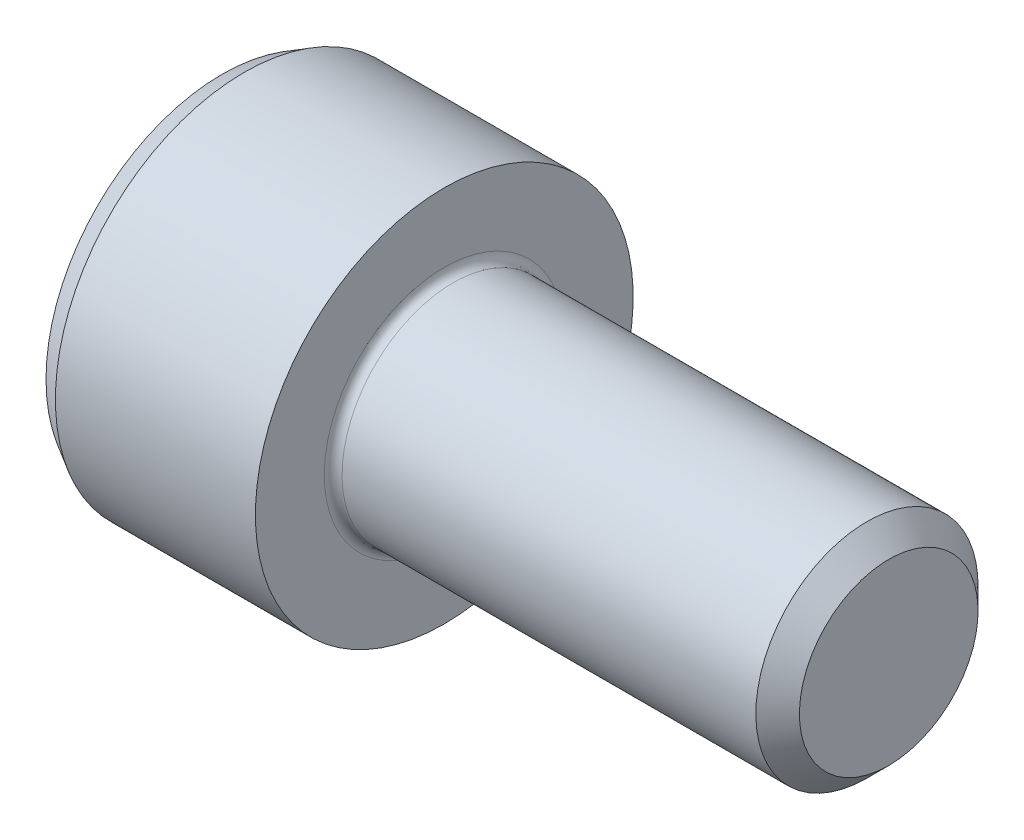
SolidWorks part; units mm, degrees
ref_plane "正面" through (0, 0, 0) normal (0, 0, 1) x (1, 0, 0)
ref_plane "平面" through (0, 0, 0) normal (0, 1, 0) x (1, 0, 0)
ref_plane "右側面" through (0, 0, 0) normal (1, 0, 0) x (0, 0, -1)
ref_plane "平面1" through (0, 0, 0) normal (0, 0, 1) x (1, 0, 0)
sketch "ｽｹｯﾁ1" plane through (0, 0, 0) normal (0, 0, 1) x (1, 0, 0)
  line L0 (-5, 0) -> (-5, 3.9613)
  line L1 (-5, 3.9613) -> (-4.5, 4.25)
  line L2 (-4.5, 4.25) -> (0, 4.25)
  line L3 (0, 4.25) -> (0, 2.7)
  line L4 (0.2, 2.5) -> (9.5095, 2.5)
  line L5 (9.5095, 2.5) -> (10, 2.0095)
  line L6 (10, 2.0095) -> (10, 0)
  line L7 (10, 0) -> (-5, 0)
  line L8 (10, 0) -> (-5, 0) construction
  arc A0 (0, 2.7) -> (0.2, 2.5) centre (0.2, 2.7) ccw
revolve "回転1" add sketch "ｽｹｯﾁ1" angle 360 about L8
cosmetic thread "ねじ山1" parameters "D1"=9.8, "D2"=4.019
ref_plane "平面2" through (0, 0, 0) normal (0, 0, 1) x (1, 0, 0)
sketch "ｽｹｯﾁ2" plane through (0, 0, 0) normal (0, 0, 1) x (1, 0, 0)
  line L0 (-5, 0) -> (-5, 2)
  line L1 (-5, 2) -> (-2.5, 2)
  line L2 (-2.5, 2) -> (-1.3453, 0)
  line L3 (-1.3453, 0) -> (-5, 0)
  line L4 (-1.3453, 0) -> (-5, 0) construction
revolve "ｶｯﾄ - 回転1" cut sketch "ｽｹｯﾁ2" angle 360 about L4
ref_plane "平面3" through (-5, 0, 0) normal (1, 0, 0) x (0, 0, -1)
sketch "ｽｹｯﾁ3" plane through (-5, 0, 0) normal (1, 0, 0) x (0, 0, -1)
  line L0 (-2, -1.1547) -> (0, -2.3094)
  line L1 (0, -2.3094) -> (2, -1.1547)
  line L2 (2, -1.1547) -> (2, 1.1547)
  line L3 (2, 1.1547) -> (0, 2.3094)
  line L4 (0, 2.3094) -> (-2, 1.1547)
  line L5 (-2, 1.1547) -> (-2, -1.1547)
extrude "ｶｯﾄ - 押し出し1" cut sketch "ｽｹｯﾁ3" along normal blind 2.5
